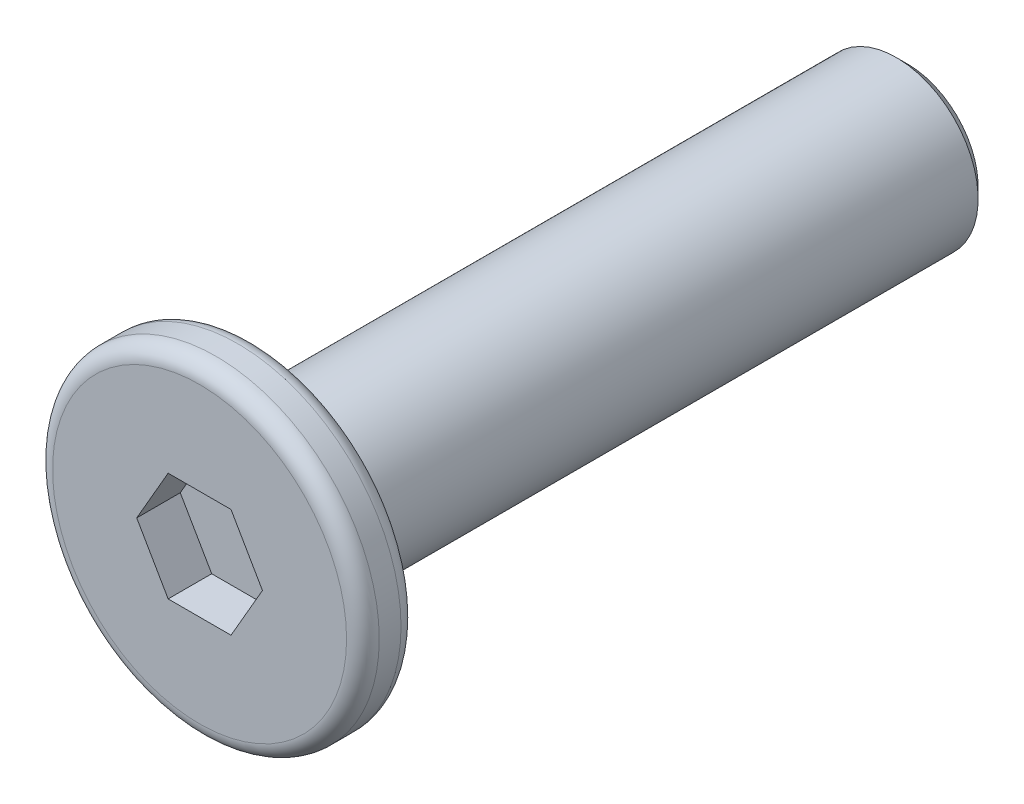
SolidWorks part; units mm, degrees
ref_plane "前视基准面" through (0, 0, 0) normal (0, 0, 1) x (1, 0, 0)
ref_plane "上视基准面" through (0, 0, 0) normal (0, 1, 0) x (1, 0, 0)
ref_plane "右视基准面" through (0, 0, 0) normal (1, 0, 0) x (0, 0, -1)
sketch "草图1" plane through (0, 0, 0) normal (0, 0, 1) x (1, 0, 0)
  circle A0 centre (0, 0) radius 3
  dimension "D1" = 6
extrude "凸台-拉伸1" add sketch "草图1" along normal mid plane 1
sketch "草图2" plane through (0, 0, -0.5) normal (0, 0, -1) x (-1, 0, 0)
  circle A0 centre (0, 0) radius 1.5
  dimension "D1" = 3
extrude "凸台-拉伸2" add sketch "草图2" along normal blind 12
chamfer "倒角1" distance 0.2 angle 45 1 edges at (-1.5, 0, -12.5)
sketch "草图3" plane through (0, 0, 0.5) normal (0, 0, 1) x (1, 0, 0)
  line L1 (1.1547, 0) -> (0.5774, 1)
  line L2 (0.5774, 1) -> (-0.5774, 1)
  line L3 (-0.5774, 1) -> (-1.1547, 0)
  line L4 (-1.1547, 0) -> (-0.5774, -1)
  line L5 (-0.5774, -1) -> (0.5774, -1)
  line L6 (0.5774, -1) -> (1.1547, 0)
  circle A0 centre (0, 0) radius 1 construction
  dimension "D1" = 2
extrude "切除-拉伸1" cut sketch "草图3" against normal blind 0.8
fillet "圆角2" radius 0.3 2 edges at (3, 0, -0.5) (3, 0, 0.5)
